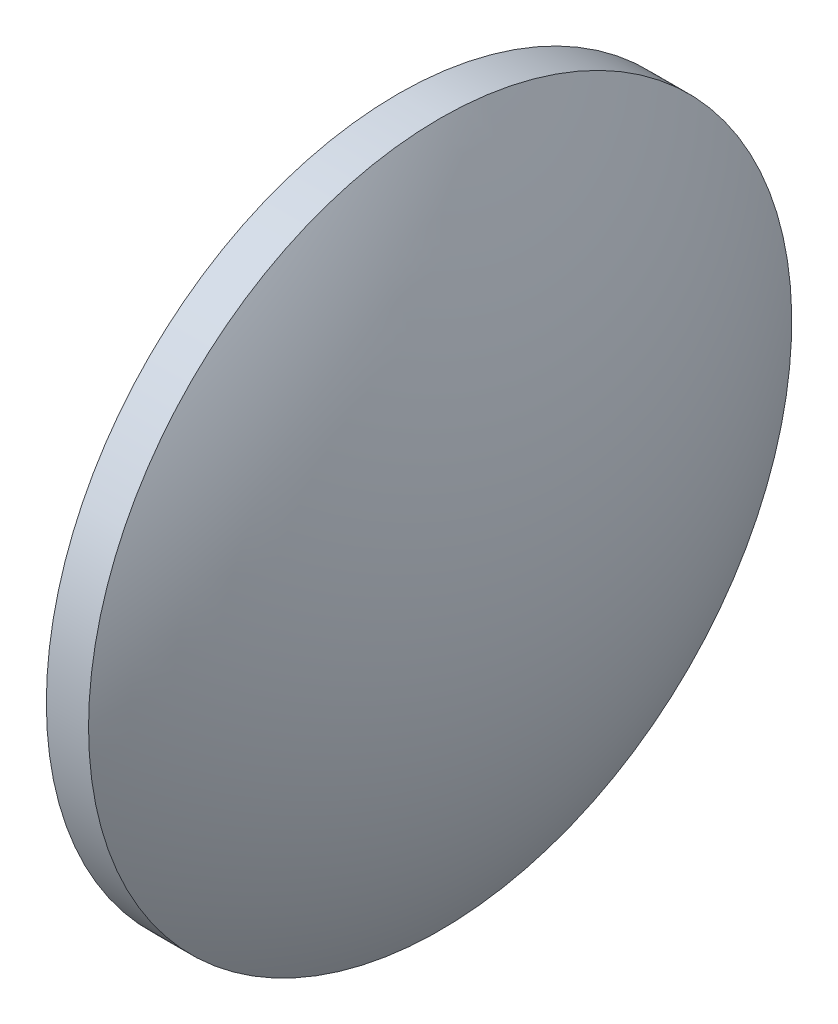
SolidWorks part; units mm, degrees
ref_plane "前视基准面" through (0, 0, 0) normal (0, 0, 1) x (1, 0, 0)
ref_plane "上视基准面" through (0, 0, 0) normal (0, 1, 0) x (1, 0, 0)
ref_plane "右视基准面" through (0, 0, 0) normal (1, 0, 0) x (0, 0, -1)
sketch "草图1" plane through (0, 0, 0) normal (0, 0, 1) x (1, 0, 0)
  line L0 (157.941, 95.701) -> (182.3353, 95.701) construction
  line L1 (168.6933, 120.701) -> (171.6933, 120.701)
  line L2 (171.6933, 120.701) -> (171.6933, 70.701)
  line L3 (171.6933, 70.701) -> (168.6933, 70.701)
  line L4 (168.6933, 70.701) -> (168.6933, 120.701)
  arc A0 (168.6933, 120.701) -> (168.6933, 70.701) centre (210.3571, 95.701) ccw
  arc A1 (171.6933, 70.701) -> (171.6933, 120.701) centre (130.0294, 95.701) ccw
  dimension "D1" = 3
  dimension "D2" = 50
revolve "旋转1" add sketch "草图1" angle 360 about L0
